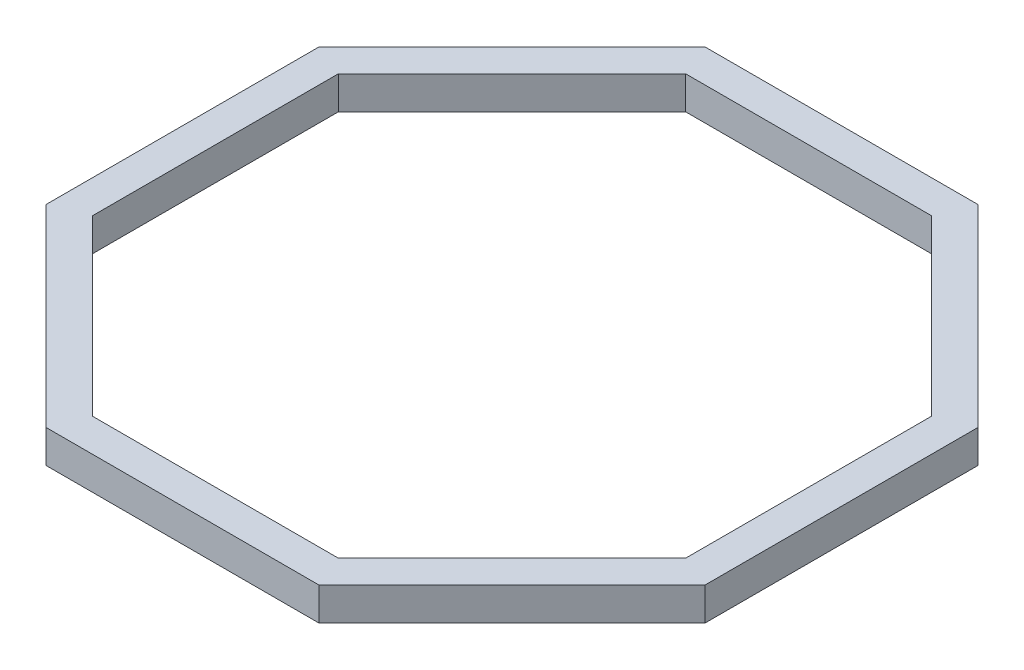
SolidWorks part; units mm, degrees
ref_plane "Alzado" through (0, 0, 0) normal (0, 0, 1) x (1, 0, 0)
ref_plane "Planta" through (0, 0, 0) normal (0, 1, 0) x (1, 0, 0)
ref_plane "Vista lateral" through (0, 0, 0) normal (1, 0, 0) x (0, 0, -1)
sketch "Croquis1" plane through (0, 0, 0) normal (0, 1, 0) x (1, 0, 0)
  line L1 (300, -124.2641) -> (300, 124.2641)
  line L2 (300, 124.2641) -> (124.2641, 300)
  line L3 (124.2641, 300) -> (-124.2641, 300)
  line L4 (-124.2641, 300) -> (-300, 124.2641)
  line L5 (-300, 124.2641) -> (-300, -124.2641)
  line L6 (-300, -124.2641) -> (-124.2641, -300)
  line L7 (-124.2641, -300) -> (124.2641, -300)
  line L8 (124.2641, -300) -> (300, -124.2641)
  line L9 (270, -111.8377) -> (270, 111.8377)
  line L10 (270, 111.8377) -> (111.8377, 270)
  line L11 (111.8377, 270) -> (-111.8377, 270)
  line L12 (-111.8377, 270) -> (-270, 111.8377)
  line L13 (-270, 111.8377) -> (-270, -111.8377)
  line L14 (-270, -111.8377) -> (-111.8377, -270)
  line L15 (-111.8377, -270) -> (111.8377, -270)
  line L16 (111.8377, -270) -> (270, -111.8377)
  circle A0 centre (0, 0) radius 300 construction
  circle A1 centre (0, 0) radius 270 construction
  dimension "D1" = 600
  dimension "D2" = 30
extrude "Saliente-Extruir1" add sketch "Croquis1" along normal blind 30
